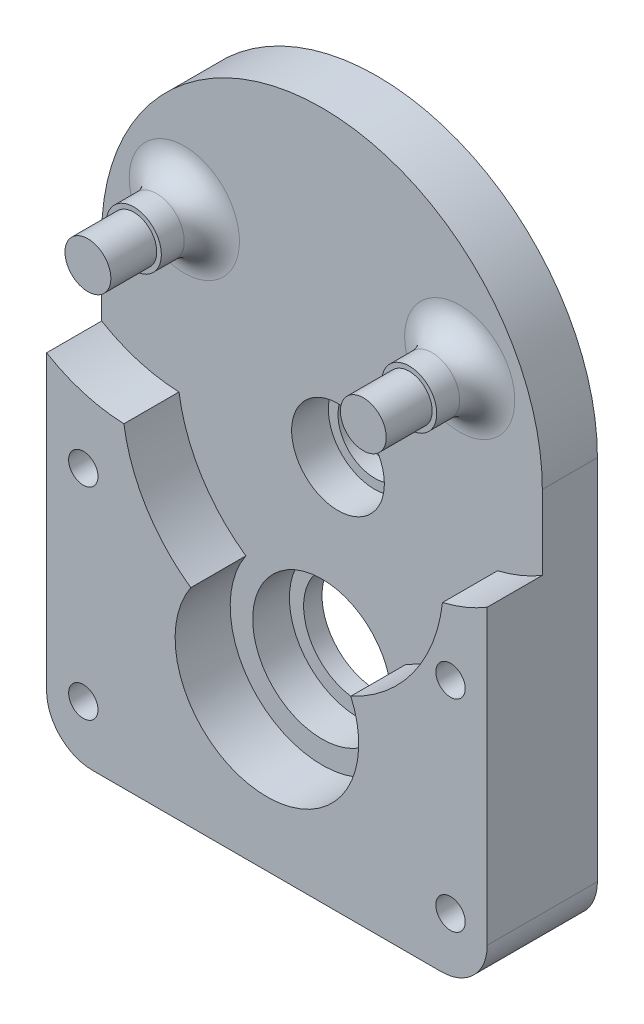
SolidWorks part; units mm, degrees
ref_plane "前视基准面" through (0, 0, 0) normal (0, 0, 1) x (1, 0, 0)
ref_plane "上视基准面" through (0, 0, 0) normal (0, 1, 0) x (1, 0, 0)
ref_plane "右视基准面" through (0, 0, 0) normal (1, 0, 0) x (0, 0, -1)
sketch "草图1" plane through (0, 0, 0) normal (0, 0, 1) x (1, 0, 0)
  line L0 (-24, 0) -> (-24, -45)
  line L1 (-24, -45) -> (24, -45)
  line L2 (24, -45) -> (24, 0)
  arc A0 (-24, 0) -> (24, 0) centre (0, 0) cw
  dimension "D1" = 24
  dimension "D2" = 45
extrude "凸台-拉伸1" add sketch "草图1" along normal blind 6
sketch "草图2" plane through (0, 0, 6) normal (0, 0, 1) x (1, 0, 0)
  line L0 (1.7431, -8.0761) -> (0, -28) construction
  line L1 (0, -28) -> (0, 0) construction
  circle A0 centre (0, -28) radius 5
  circle A1 centre (1.7431, -8.0761) radius 15
  circle A2 centre (-15, 6.899) radius 15
  circle A3 centre (15, 6.899) radius 15
  circle A4 centre (1.7431, -8.0761) radius 5
  dimension "D2" = 30
  dimension "D3" = 10
  dimension "D5" = 30
  dimension "D6" = 10
  dimension "D1" = 28
  dimension "D4" = 5
sketch "草图3" plane through (0, 0, 6) normal (0, 0, 1) x (1, 0, 0)
  circle A0 centre (-15, 6.899) radius 3
  circle A1 centre (15, 6.899) radius 3
  dimension "D1" = 6
extrude "凸台-拉伸2" add sketch "草图3" along normal blind 5.5
sketch "草图4" plane through (0, 0, 11.5) normal (0, 0, 1) x (1, 0, 0)
  circle A0 centre (-15, 6.899) radius 2.5
  circle A1 centre (15, 6.899) radius 2.5
  dimension "D1" = 5
extrude "凸台-拉伸3" add sketch "草图4" along normal blind 5
sketch "草图5" plane through (0, 0, 6) normal (0, 0, 1) x (1, 0, 0)
  circle A0 centre (1.7431, -8.0761) radius 5.05
  dimension "D1" = 10.1
extrude "切除-拉伸1" cut sketch "草图5" against normal blind 4
sketch "草图6" plane through (0, 0, 2) normal (0, 0, 1) x (1, 0, 0)
  circle A0 centre (1.7431, -8.0761) radius 4
  dimension "D1" = 8
extrude "切除-拉伸2" cut sketch "草图6" against normal through all
sketch "草图7" plane through (0, 0, 6) normal (0, 0, 1) x (1, 0, 0)
  circle A0 centre (0, -28) radius 7.55
  dimension "D1" = 15.1
extrude "切除-拉伸3" cut sketch "草图7" against normal blind 4
sketch "草图8" plane through (0, 0, 2) normal (0, 0, 1) x (1, 0, 0)
  circle A0 centre (0, -28) radius 6
  dimension "D1" = 12
extrude "切除-拉伸4" cut sketch "草图8" against normal through all
fillet "圆角1" radius 3 2 edges at (12, 6.899, 6) (-18, 6.899, 6)
sketch "草图9" plane through (0, 0, 6) normal (0, 0, 1) x (1, 0, 0)
  line L0 (24, -45) -> (24, 0) construction
  line L1 (-24, -45) -> (24, -45) construction
  line L2 (-24, 0) -> (-24, -45) construction
  line L3 (24, -45) -> (24, -8.1093)
  line L4 (-24, -45) -> (24, -45)
  line L5 (-24, -8.1093) -> (-24, -45)
  arc A0 (-15.5752, -10.5915) -> (-8.2932, -22.4122) centre (1.7431, -8.0761) ccw
  arc A1 (-8.2932, -22.4122) -> (9.1375, -23.9372) centre (0, -28) ccw
  arc A2 (-24, -8.1093) -> (-15.5752, -10.5915) centre (-15, 6.899) ccw
  arc A3 (19.1248, -10.1079) -> (24, -8.1093) centre (15, 6.899) ccw
  arc A4 (9.1375, -23.9372) -> (19.1248, -10.1079) centre (1.7431, -8.0761) ccw
  dimension "D1" = 35
  dimension "D2" = 20
extrude "凸台-拉伸4" add sketch "草图9" along normal blind 6
sketch "草图10" plane through (0, 0, 0) normal (0, 0, -1) x (-1, 0, 0)
  line L0 (0, -28) -> (-35.362, -28) construction
  line L1 (0, -28) -> (0, 0) construction
  line L2 (0, -28) -> (0, 0) construction
  line L3 (-24, -45) -> (-24, 0) construction
  line L4 (24, -45) -> (-24, -45) construction
  circle A0 centre (-20, -39) radius 1.6
  circle A1 centre (-20, -17) radius 1.6
  circle A2 centre (20, -39) radius 1.6
  circle A3 centre (20, -17) radius 1.6
  dimension "D3" = 3.2
  dimension "D1" = 4
  dimension "D2" = 6
extrude "切除-拉伸5" cut sketch "草图10" against normal through all
sketch "草图11" plane through (0, 0, 0) normal (0, 0, -1) x (-1, 0, 0)
  circle A0 centre (-20, -17) radius 2.1
  circle A1 centre (-20, -39) radius 2.1
  circle A2 centre (20, -17) radius 2.1
  circle A3 centre (20, -39) radius 2.1
  dimension "D1" = 4.2
extrude "切除-拉伸6" cut sketch "草图11" against normal blind 6
fillet "圆角2" radius 5 2 edges at (24, -45, 6) (-24, -45, 6)
